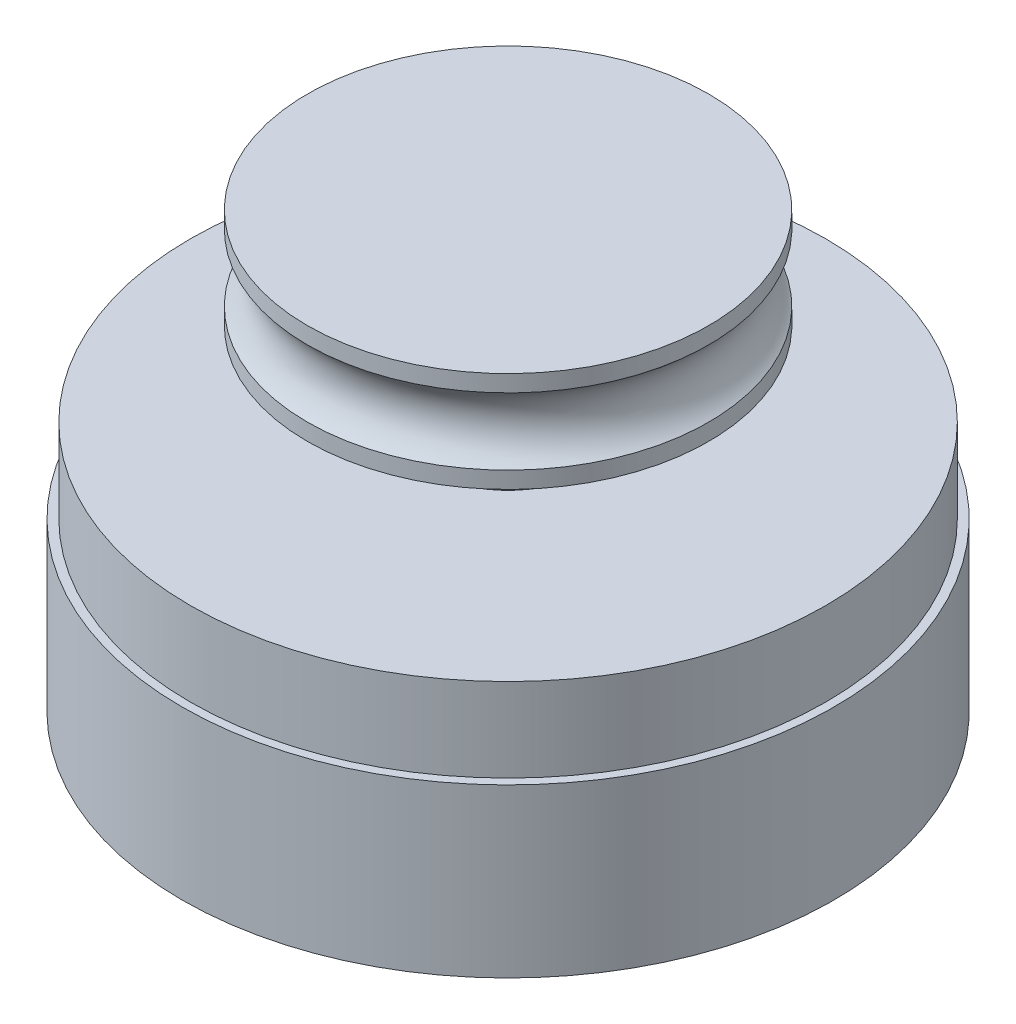
SolidWorks part; units mm, degrees
ref_plane "前视基准面" through (0, 0, 0) normal (0, 0, 1) x (1, 0, 0)
ref_plane "上视基准面" through (0, 0, 0) normal (0, 1, 0) x (1, 0, 0)
ref_plane "右视基准面" through (0, 0, 0) normal (1, 0, 0) x (0, 0, -1)
sketch "草图1" plane through (0, 0, 0) normal (0, 1, 0) x (1, 0, 0)
  circle A0 centre (0, 0) radius 19.5
  dimension "D1" = 39
extrude "凸台-拉伸1" add sketch "草图1" along normal blind 10
sketch "草图2" plane through (0, 10, 0) normal (0, 1, 0) x (1, 0, 0)
  circle A0 centre (0, 0) radius 19
  dimension "D1" = 38
extrude "凸台-拉伸2" add sketch "草图2" along normal blind 5
sketch "草图3" plane through (0, 15, 0) normal (0, 1, 0) x (1, 0, 0)
  circle A0 centre (0, 0) radius 5
  dimension "D1" = 10
extrude "凸台-拉伸3" add sketch "草图3" along normal blind 5
sketch "草图5" plane through (0, 0, 0) normal (0, 0, 1) x (1, 0, 0)
  line L0 (0, 20) -> (0, 26)
  line L1 (5, 20) -> (-5, 20) construction
  line L2 (0, 26) -> (12, 26)
  line L3 (12, 20) -> (0, 20)
  line L4 (12, 20) -> (12, 21)
  line L5 (12, 26) -> (12, 25)
  arc A1 (12, 21) -> (12, 25) centre (13.5, 23) cw
  dimension "D3" = 2.5
  dimension "D1" = 6
  dimension "D2" = 1
  dimension "D4" = 12
revolve "旋转1" add sketch "草图5" angle 360 about L0
